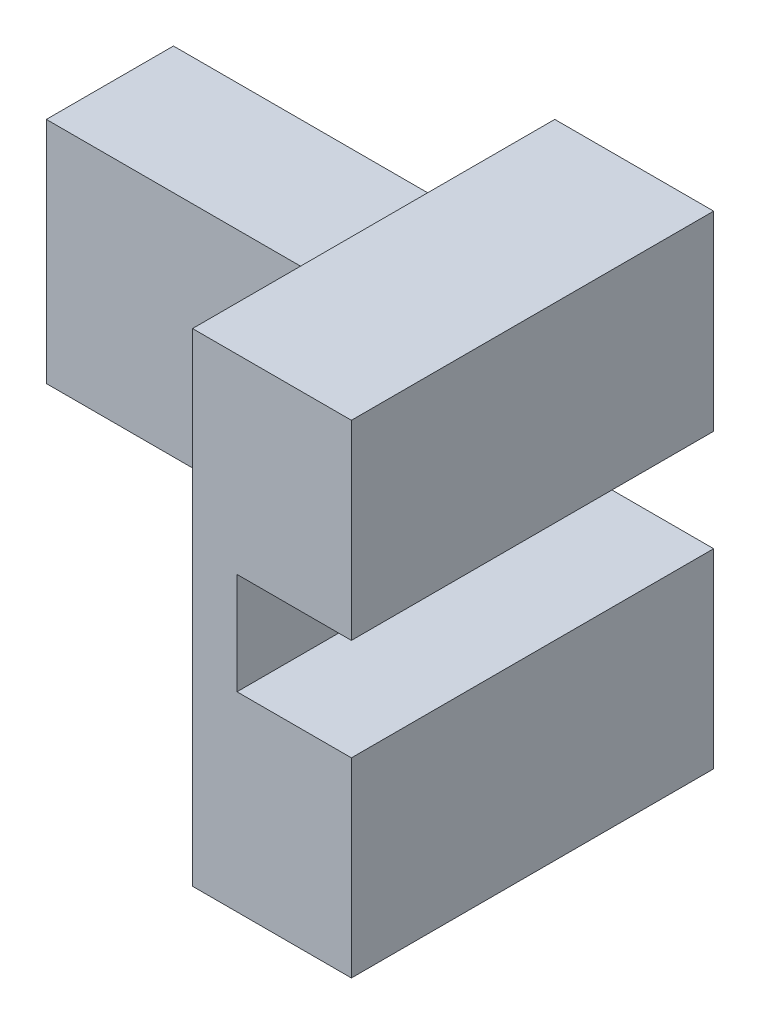
SolidWorks part; units mm, degrees
ref_plane "Front" through (0, 0, 0) normal (0, 0, 1) x (1, 0, 0)
ref_plane "Top" through (0, 0, 0) normal (0, 1, 0) x (1, 0, 0)
ref_plane "Right" through (0, 0, 0) normal (1, 0, 0) x (0, 0, -1)
sketch "Sketch1" plane through (0, 0, 0) normal (0, 0, 1) x (1, 0, 0)
  line L0 (-14.2593, 17.2489) -> (-14.2593, 15.6489)
  line L1 (-14.2593, 17.2489) -> (-12.4593, 17.2489)
  line L2 (-14.2593, 15.6489) -> (-12.4593, 15.6489)
  line L9 (-14.9593, 14.6489) -> (-14.9593, 12.6489)
  line L14 (-12.4593, 15.6489) -> (-12.4593, 12.6489)
  line L15 (-12.4593, 12.6489) -> (-14.9593, 12.6489)
  line L16 (-14.9593, 14.6489) -> (-20.9593, 14.6489)
  line L17 (-12.4593, 17.2489) -> (-12.4593, 20.2489)
  line L18 (-12.4593, 20.2489) -> (-14.9593, 20.2489)
  line L19 (-14.9593, 20.2489) -> (-14.9593, 18.2489)
  line L20 (-14.9593, 18.2489) -> (-20.9593, 18.2489)
  line L21 (-20.9593, 18.2489) -> (-20.9593, 14.6489)
  dimension "D1" = 1.6
  dimension "D2" = 1.8
extrude "Boss-Extrude1" add sketch "Sketch1" along normal blind 2
sketch "Sketch2" plane through (0, 0, 2) normal (0, 0, 1) x (1, 0, 0)
  line L0 (-14.9593, 20.2489) -> (-12.4593, 20.2489)
  line L1 (-12.4593, 20.2489) -> (-12.4593, 17.2489)
  line L2 (-12.4593, 17.2489) -> (-14.2593, 17.2489)
  line L3 (-14.2593, 17.2489) -> (-14.2593, 15.6489)
  line L4 (-14.2593, 15.6489) -> (-12.4593, 15.6489)
  line L5 (-12.4593, 15.6489) -> (-12.4593, 12.6489)
  line L6 (-12.4593, 12.6489) -> (-14.9593, 12.6489)
  line L7 (-14.9593, 12.6489) -> (-14.9593, 20.2489)
extrude "Boss-Extrude2" add sketch "Sketch2" along normal blind 3.7
